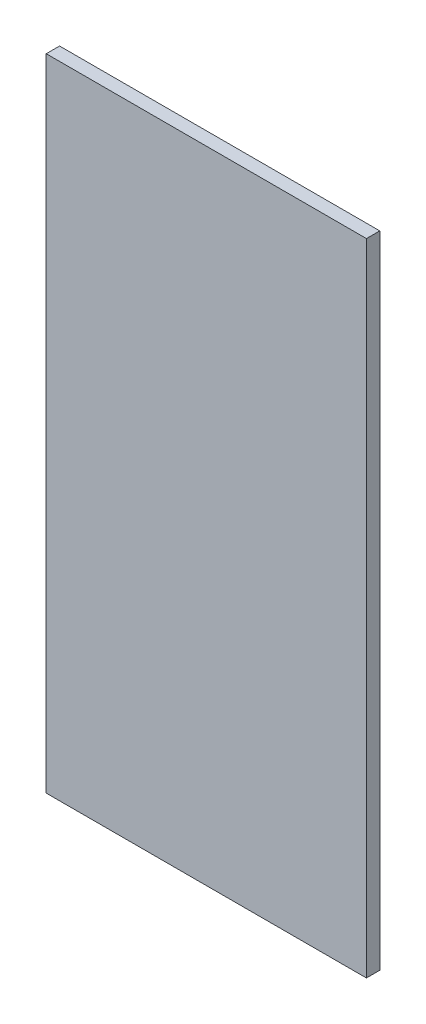
SolidWorks part; units mm, degrees
ref_plane "Front Plane" through (0, 0, 0) normal (0, 0, 1) x (1, 0, 0)
ref_plane "Top Plane" through (0, 0, 0) normal (0, 1, 0) x (1, 0, 0)
ref_plane "Right Plane" through (0, 0, 0) normal (1, 0, 0) x (0, 0, -1)
sketch "Sketch1" plane through (0, 0, 0) normal (0, 0, 1) x (1, 0, 0)
  line L1 (0, 0) -> (609.6, 0)
  line L2 (0, 0) -> (0, -1219.2)
  line L3 (0, -1219.2) -> (609.6, -1219.2)
  line L4 (609.6, 0) -> (609.6, -1219.2)
  dimension "D1" = 1219.2
  dimension "D2" = 609.6
extrude "Boss-Extrude1" add sketch "Sketch1" along normal blind 25.4
